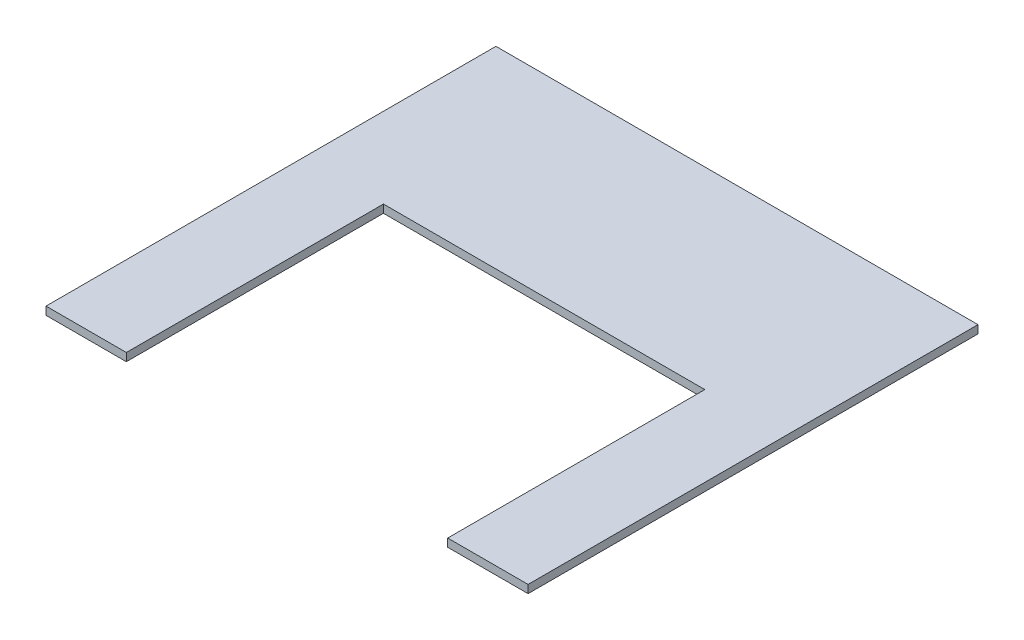
SolidWorks part; units mm, degrees
ref_plane "Front Plane" through (0, 0, 0) normal (0, 0, 1) x (1, 0, 0)
ref_plane "Top Plane" through (0, 0, 0) normal (0, 1, 0) x (1, 0, 0)
ref_plane "Right Plane" through (0, 0, 0) normal (1, 0, 0) x (0, 0, -1)
sketch "Sketch1" plane through (0, 0, 0) normal (0, 1, 0) x (1, 0, 0)
  line L1 (0, 0) -> (381, 0)
  line L2 (0, 0) -> (0, 429.26)
  line L3 (0, 429.26) -> (381, 429.26)
  line L4 (381, 0) -> (381, 429.26)
  dimension "D1" = 429.26
  dimension "D2" = 381
extrude "Boss-Extrude1" add sketch "Sketch1" along normal blind 6.35
sketch "Sketch2" plane through (0, 6.35, 0) normal (0, 1, 0) x (1, 0, 0)
  line L0 (0, 0) -> (381, 0) construction
  line L1 (63.5, 203.2) -> (317.5, 203.2)
  line L2 (63.5, 203.2) -> (63.5, 0)
  line L3 (63.5, 0) -> (317.5, 0)
  line L4 (317.5, 203.2) -> (317.5, 0)
  line L5 (381, 0) -> (381, 429.26) construction
  dimension "D1" = 254
  dimension "D2" = 203.2
  dimension "D3" = 0
  dimension "D4" = 63.5
extrude "Cut-Extrude1" cut sketch "Sketch2" against normal blind 6.35
sketch "Sketch3" plane through (0, 6.35, 0) normal (0, 1, 0) x (1, 0, 0)
  line L0 (381, 0) -> (381, 429.26) construction
  line L1 (0, 0) -> (381, 0)
  line L2 (0, 0) -> (0, 73.66)
  line L3 (0, 73.66) -> (381, 73.66)
  line L4 (381, 0) -> (381, 73.66)
  dimension "D1" = 73.66
extrude "Cut-Extrude2" cut sketch "Sketch3" against normal blind 6.35
sketch "Sketch4" plane through (0, 0, -203.2) normal (0, 0, 1) x (1, 0, 0)
  line L0 (317.5, 6.35) -> (63.5, 6.35) construction
  line L1 (63.5, 0) -> (317.5, 0)
  line L2 (63.5, 0) -> (63.5, 6.35)
  line L3 (63.5, 6.35) -> (317.5, 6.35)
  line L4 (317.5, 0) -> (317.5, 6.35)
  line L5 (63.5, 0) -> (63.5, 6.35) construction
  line L6 (317.5, 0) -> (63.5, 0) construction
  dimension "D1" = 254
  dimension "D2" = 0
  dimension "D3" = 0
extrude "Cut-Extrude3" cut sketch "Sketch4" against normal blind 73.66
